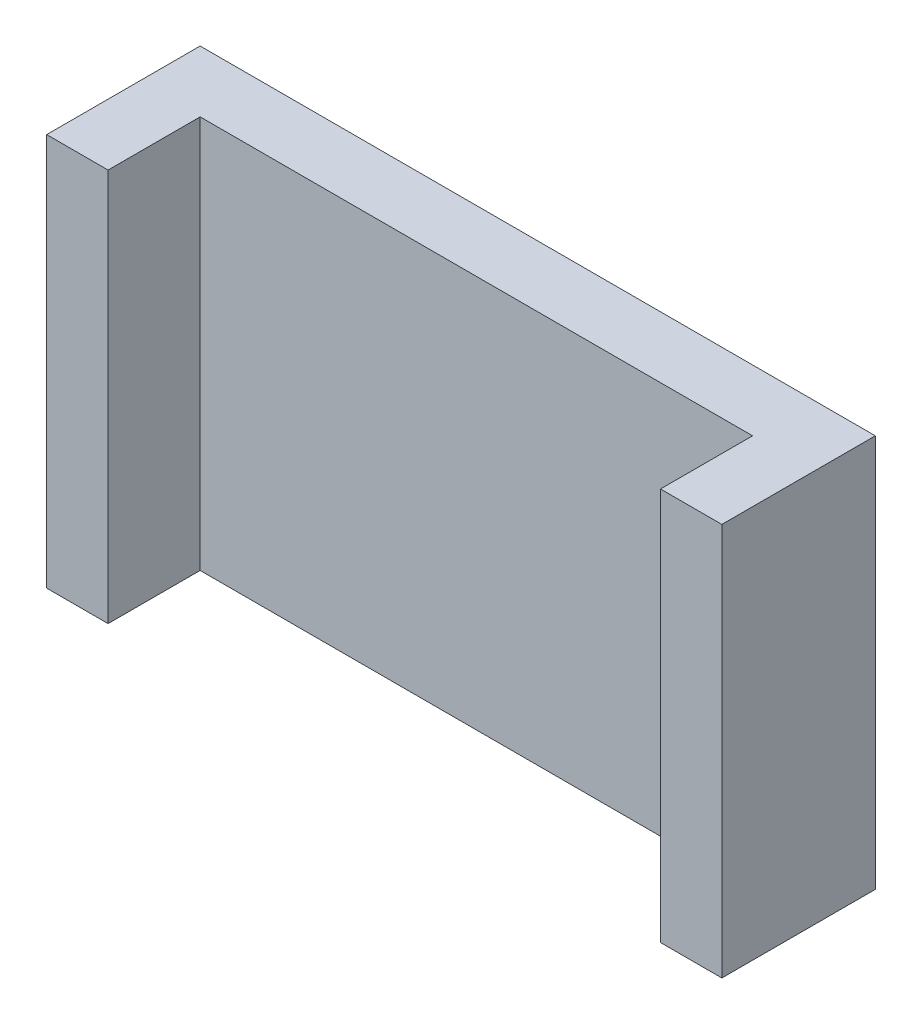
SolidWorks part; units mm, degrees
ref_plane "Front Plane" through (0, 0, 0) normal (0, 0, 1) x (1, 0, 0)
ref_plane "Top Plane" through (0, 0, 0) normal (0, 1, 0) x (1, 0, 0)
ref_plane "Right Plane" through (0, 0, 0) normal (1, 0, 0) x (0, 0, -1)
sketch "Sketch1" plane through (0, 0, 0) normal (0, 0, 1) x (1, 0, 0)
  line L1 (0, 0) -> (55, 0)
  line L2 (0, 0) -> (0, 32)
  line L3 (0, 32) -> (55, 32)
  line L4 (55, 0) -> (55, 32)
extrude "Boss-Extrude1" add sketch "Sketch1" along normal blind 5 contours L3 L4 L1 L2
sketch "Sketch2" plane through (0, 0, 5) normal (0, 0, 1) x (1, 0, 0)
  line L0 (0, 0) -> (55, 0) construction
  line L1 (0, 32) -> (5, 32)
  line L2 (0, 32) -> (0, 0)
  line L3 (0, 0) -> (5, 0)
  line L4 (5, 32) -> (5, 0)
  line L10 (55, 32) -> (50, 32)
  line L11 (55, 32) -> (55, 0)
  line L12 (55, 0) -> (50, 0)
  line L13 (50, 32) -> (50, 0)
  line M9 (0, 32) -> (0, 0)
  line M10 (0, 0) -> (55, 0)
  line M12 (55, 32) -> (0, 32)
extrude "Boss-Extrude2" add sketch "Sketch2" along normal blind 7.5 contours L4 M12 M9 M10 | L10 L13 L12 L11
